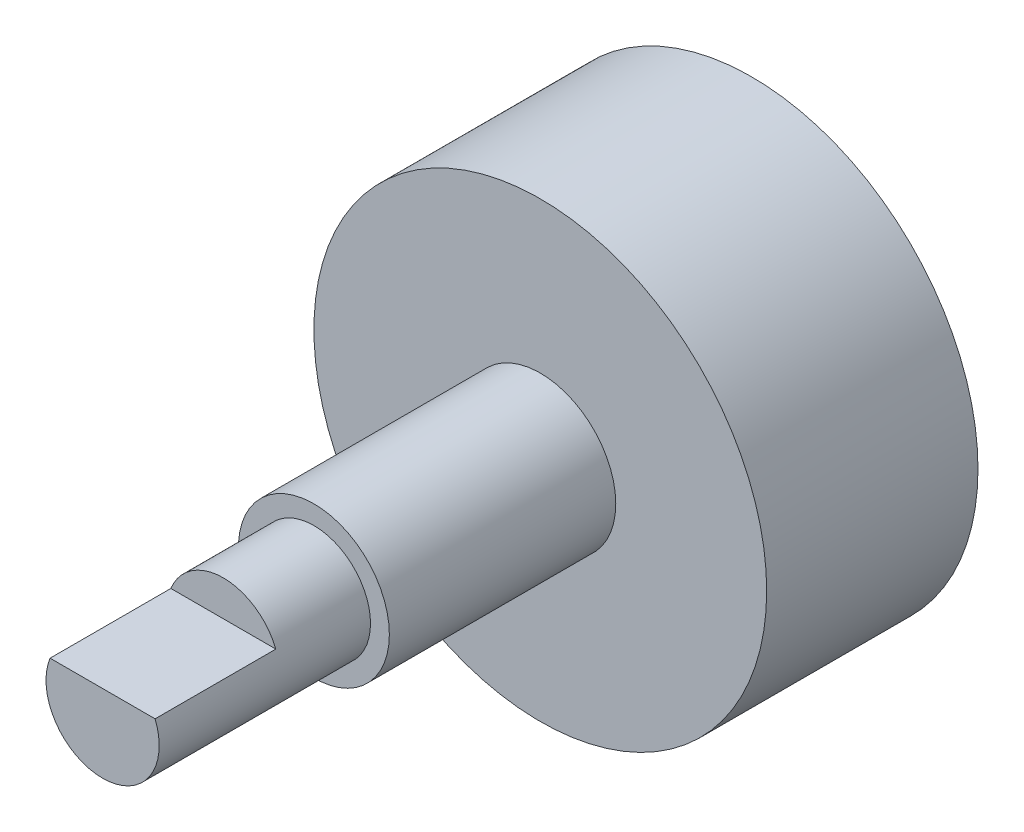
SolidWorks part; units mm, degrees
material "Plain Carbon Steel"
ref_plane "Front Plane" through (0, 0, 0) normal (0, 0, 1) x (1, 0, 0)
ref_plane "Top Plane" through (0, 0, 0) normal (0, 1, 0) x (1, 0, 0)
ref_plane "Right Plane" through (0, 0, 0) normal (1, 0, 0) x (0, 0, -1)
sketch "Sketch1" plane through (0, 0, 0) normal (0, 0, 1) x (1, 0, 0)
  circle A0 centre (0, 0) radius 9.525
  dimension "D1" = 19.05
extrude "Boss-Extrude1" add sketch "Sketch1" against normal blind 8.89
sketch "Sketch2" plane through (0, 0, 0) normal (0, 0, 1) x (1, 0, 0)
  circle A0 centre (0, 0) radius 3.175
  dimension "D1" = 6.35
extrude "Boss-Extrude2" add sketch "Sketch2" along normal blind 9.525
sketch "Sketch3" plane through (0, 0, 9.525) normal (0, 0, 1) x (1, 0, 0)
  circle A0 centre (0, 0) radius 2.3813
  dimension "D1" = 4.7625
extrude "Boss-Extrude3" add sketch "Sketch3" along normal blind 8.89
sketch "Sketch4" plane through (0, 0, 18.415) normal (0, 0, 1) x (1, 0, 0)
  line L0 (-4.27, 0.889) -> (4.27, 0.889)
  line L1 (0, -10.4775) -> (0, 10.4775) construction
  line L2 (10.4775, 0) -> (-10.4775, 0) construction
  arc A0 (4.27, 0.889) -> (-4.27, 0.889) centre (0, 0.889) ccw
  dimension "D1" = 0.889
extrude "Cut-Extrude1" cut sketch "Sketch4" against normal blind 5.08
